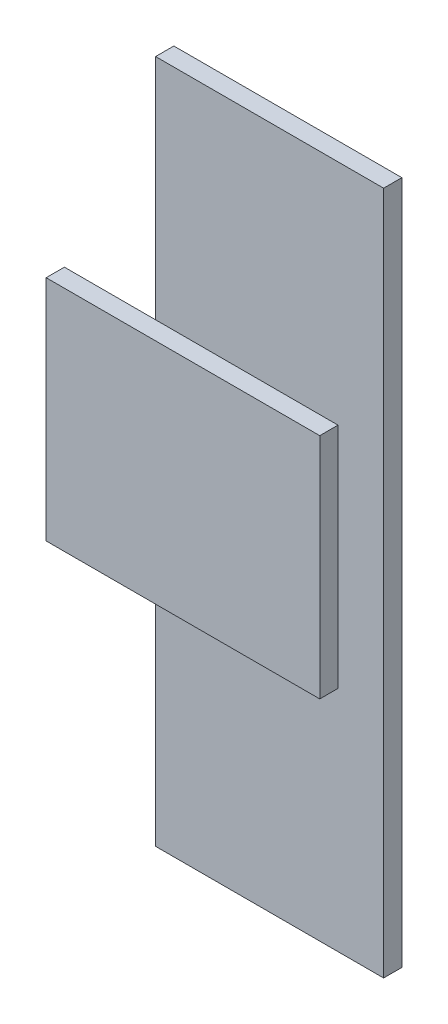
SolidWorks part; units mm, degrees
material "Cardboard"
ref_plane "Front Plane" through (0, 0, 0) normal (0, 0, 1) x (1, 0, 0)
ref_plane "Top Plane" through (0, 0, 0) normal (0, 1, 0) x (1, 0, 0)
ref_plane "Right Plane" through (0, 0, 0) normal (1, 0, 0) x (0, 0, -1)
sketch "Sketch1" plane through (0, 0, 0) normal (0, 0, 1) x (1, 0, 0)
  line L1 (0, 0) -> (50, 0)
  line L2 (0, 0) -> (0, 150)
  line L3 (0, 150) -> (50, 150)
  line L4 (50, 0) -> (50, 150)
  dimension "D1" = 150
  dimension "D2" = 50
extrude "Boss-Extrude1" add sketch "Sketch1" along normal blind 4
sketch "Sketch2" plane through (0, 0, 4) normal (0, 0, 1) x (1, 0, 0)
  line L0 (0, 150) -> (0, 0) construction
  line L1 (-20, 100) -> (40, 100)
  line L2 (-20, 100) -> (-20, 50)
  line L3 (-20, 50) -> (40, 50)
  line L4 (40, 100) -> (40, 50)
  point P6 (0, 75)
  point P7 (-20, 75)
  dimension "D1" = 40
  dimension "D2" = 20
  dimension "D3" = 50
extrude "Boss-Extrude2" add sketch "Sketch2" along normal blind 4
